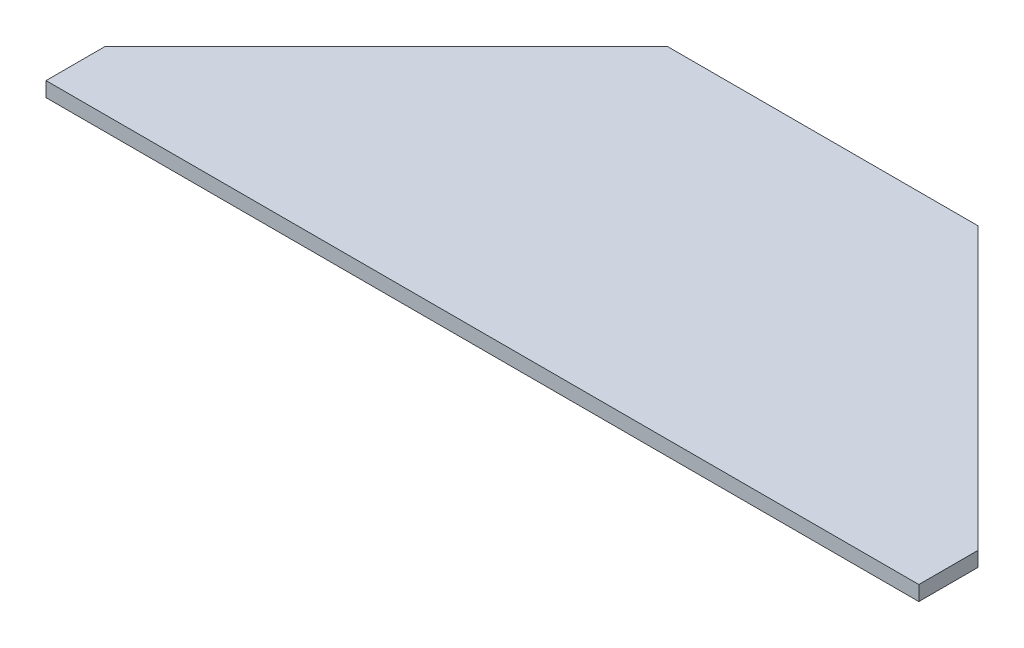
SolidWorks part; units mm, degrees
ref_plane "Front Plane" through (0, 0, 0) normal (0, 0, 1) x (1, 0, 0)
ref_plane "Top Plane" through (0, 0, 0) normal (0, 1, 0) x (1, 0, 0)
ref_plane "Right Plane" through (0, 0, 0) normal (1, 0, 0) x (0, 0, -1)
sketch "Sketch1" plane through (0, 0, 0) normal (0, 1, 0) x (1, 0, 0)
  line L0 (0, 0) -> (374.65, 0)
  line L1 (374.65, 0) -> (374.65, 25.4)
  line L2 (374.65, 25.4) -> (254, 146.05)
  line L3 (254, 146.05) -> (120.65, 146.05)
  line L4 (120.65, 146.05) -> (0, 25.4)
  line L5 (0, 25.4) -> (0, 0)
  point P9 (187.325, 0)
  point P10 (187.325, 146.05)
  dimension "D1" = 120.65
  dimension "D2" = 374.65
  dimension "D3" = 25.4
  dimension "D4" = 146.05
  dimension "D5" = 120.65
  dimension "D6" = 133.35
extrude "Boss-Extrude1" add sketch "Sketch1" along normal blind 6.35
ref_plane "back" through (0, 0, -25.4) normal (0, 0, -1) x (-1, 0, 0)
ref_plane "mid" through (0, 3.175, 0) normal (0, -1, 0) x (-1, 0, 0)
ref_plane "center" through (187.325, 0, 0) normal (-1, 0, 0) x (0, 0, 1)
